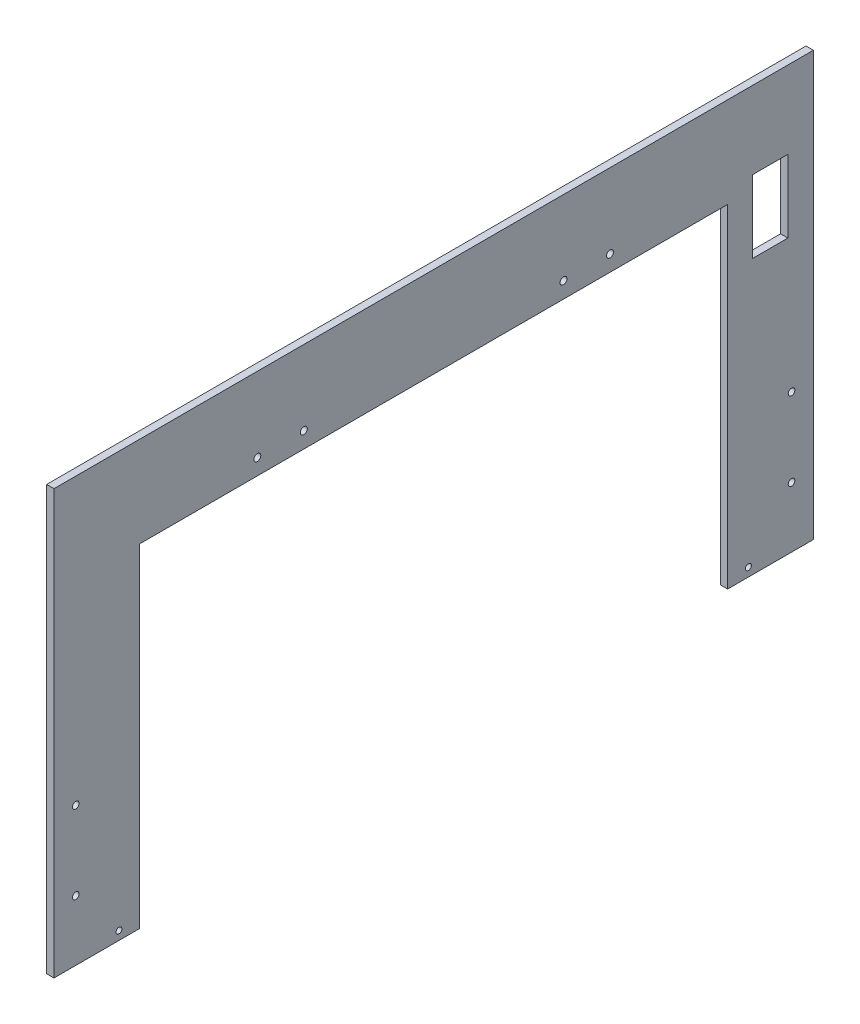
SolidWorks part; units mm, degrees
ref_plane "Front Plane" through (0, 0, 0) normal (0, 0, 1) x (1, 0, 0)
ref_plane "Top Plane" through (0, 0, 0) normal (0, 1, 0) x (1, 0, 0)
ref_plane "Right Plane" through (0, 0, 0) normal (1, 0, 0) x (0, 0, -1)
sketch "Sketch1" plane through (0, 0, 0) normal (1, 0, 0) x (0, 0, -1)
  line L1 (-246.0625, -137.3187) -> (246.0625, -137.3187)
  line L2 (-246.0625, -137.3187) -> (-246.0625, 137.3188)
  line L3 (-246.0625, 137.3188) -> (246.0625, 137.3188)
  line L4 (246.0625, -137.3187) -> (246.0625, 137.3188)
  line L5 (-246.0625, -137.3187) -> (246.0625, 137.3188) construction
  line L6 (-246.0625, 137.3188) -> (246.0625, -137.3187) construction
  point P0 (0, 0)
  dimension "D1" = 274.6375
  dimension "D2" = 492.125
extrude "Boss-Extrude1" add sketch "Sketch1" along normal blind 4.7625
sketch "Sketch2" plane through (4.7625, 0, 0) normal (1, 0, 0) x (0, 0, -1)
  line L0 (0, 0) -> (42.4264, 42.4264) construction
  line L1 (-24.8528, -60) -> (24.8528, -60)
  line L2 (-60, -24.8528) -> (-60, 24.8528)
  line L3 (-24.8528, 60) -> (24.8528, 60)
  line L4 (60, -24.8528) -> (60, 24.8528)
  line L5 (-42.4264, -42.4264) -> (42.4264, 42.4264) construction
  line L6 (0, 0) -> (-42.4264, 42.4264) construction
  line L7 (-42.4264, 42.4264) -> (-24.8528, 60) construction
  line L8 (0, 0) -> (42.4264, -42.4264) construction
  line L9 (-42.4264, 42.4264) -> (-60, 24.8528) construction
  line L10 (42.4264, -42.4264) -> (24.8528, -60) construction
  line L11 (42.4264, -42.4264) -> (60, -24.8528) construction
  line L12 (0, 0) -> (0, 60) construction
  line L13 (0, 0) -> (0, -60) construction
  line L14 (42.4264, 42.4264) -> (60, 24.8528) construction
  line L15 (42.4264, 42.4264) -> (24.8528, 60) construction
  line L16 (-42.4264, -42.4264) -> (-24.8528, -60) construction
  line L17 (-42.4264, -42.4264) -> (-60, -24.8528) construction
  line L18 (-24.8528, 60) -> (-60, 24.8528)
  line L19 (24.8528, 60) -> (60, 24.8528)
  line L20 (42.4264, -42.4264) -> (60, -24.8528)
  line L21 (24.8528, -60) -> (42.4264, -42.4264)
  line L22 (-60, -24.8528) -> (-24.8528, -60)
  point P0 (0, 0)
  dimension "D2" = 60
extrude "Cut-Extrude1" cut sketch "Sketch2" against normal up to next
sketch "Sketch3" plane through (0, 0, 246.0625) normal (0, 0, 1) x (1, 0, 0)
  line L1 (0, 137.3188) -> (4.7625, 137.3188)
  line L2 (0, 137.3188) -> (0, -137.3187)
  line L3 (0, -137.3187) -> (4.7625, -137.3187)
  line L4 (4.7625, 137.3188) -> (4.7625, -137.3187)
extrude "Boss-Extrude2" add sketch "Sketch3" against normal up to next
hole_wizard "#8 Clearance Hole1" positions "Sketch5" profile "Sketch4" hole size "#8" standard "ANSI Inch"
sketch "Sketch5" plane through (4.7625, 0, 0) normal (1, 0, 0) x (0, 0, -1)
  line L1 (-246.0625, 137.3188) -> (-246.0625, -137.3187) construction
  line L2 (-246.0625, -137.3187) -> (246.0625, -137.3187) construction
  line L3 (246.0625, -137.3187) -> (246.0625, 137.3188) construction
  point P0 (-231.9338, -98.2027)
  point P2 (-231.9338, -47.4027)
  point P4 (231.9337, -47.4027)
  point P6 (231.9337, -98.2027)
  dimension "D1" = 14.1287
  dimension "D2" = 89.916
  dimension "D3" = 39.116
  dimension "D4" = 14.1288
sketch "Sketch4" plane through (4.7625, -98.2027, 231.9338) normal (0, 1, 0) x (0, 0, -1)
  line L0 (0, 0) -> (0, 75.7154)
  line L1 (0, 75.7154) -> (2.1526, 74.422)
  line L2 (2.1526, 74.422) -> (2.1526, 0)
  line L5 (2.1526, 0) -> (0, 0)
  line L10 (0, 75.7154) -> (-2.1527, 74.422) construction
  line L11 (0, -6.35) -> (0, 107.95) construction
  dimension "Hole Dia." = 4.3053
  dimension "Hole Depth" = 74.422
  dimension "Drill Angle" = 118
sketch "Sketch9" plane through (4.7625, 0, 0) normal (1, 0, 0) x (0, 0, -1)
  line L0 (-246.0625, -137.3187) -> (246.0625, -137.3187) construction
  line L1 (-190.5, -137.3187) -> (190.5, -137.3187)
  line L2 (-190.5, -137.3187) -> (-190.5, 78.5813)
  line L3 (-190.5, 78.5813) -> (190.5, 78.5813)
  line L4 (190.5, -137.3187) -> (190.5, 78.5813)
  point P6 (0, 78.5813)
  dimension "D1" = 381
  dimension "D2" = 215.9
extrude "Cut-Extrude2" cut sketch "Sketch9" against normal through all
hole_wizard "#8 Clearance Hole2" positions "Sketch11" profile "Sketch10" hole size "#8" standard "ANSI Inch"
sketch "Sketch11" plane through (4.7625, 0, 0) normal (1, 0, 0) x (0, 0, -1)
  line L0 (-190.5, 78.5813) -> (-190.5, -137.3187) construction
  line L1 (190.5, -137.3187) -> (190.5, 78.5813) construction
  line L2 (190.5, 78.5813) -> (-190.5, 78.5813) construction
  point P0 (-114.3, 88.9)
  point P2 (-84.1375, 88.9)
  point P4 (84.1375, 88.9)
  point P6 (114.3, 88.9)
  dimension "D1" = 76.2
  dimension "D2" = 30.1625
  dimension "D3" = 30.1625
  dimension "D4" = 76.2
  dimension "D5" = 10.3187
sketch "Sketch10" plane through (4.7625, 88.9, 114.3) normal (0, 1, 0) x (0, 0, -1)
  line L0 (0, 0) -> (0, 75.7727)
  line L1 (0, 75.7727) -> (2.2479, 74.422)
  line L2 (2.2479, 74.422) -> (2.2479, 0)
  line L5 (2.2479, 0) -> (0, 0)
  line L10 (0, 75.7727) -> (-2.2479, 74.422) construction
  line L11 (0, -6.35) -> (0, 107.95) construction
  dimension "Hole Dia." = 4.4958
  dimension "Hole Depth" = 74.422
  dimension "Drill Angle" = 118
hole_wizard "#6 Clearance Hole1" positions "Sketch13" profile "Sketch12" hole size "#6" standard "ANSI Inch"
sketch "Sketch13" plane through (4.7625, 0, 0) normal (1, 0, 0) x (0, 0, -1)
  line L0 (-246.0625, -137.3187) -> (-190.5, -137.3187) construction
  line L1 (-190.5, 78.5813) -> (-190.5, -137.3187) construction
  line L2 (190.5, -137.3187) -> (190.5, 78.5813) construction
  point P0 (-203.9709, -131.7307)
  point P2 (203.9709, -131.7307)
  dimension "D1" = 5.588
  dimension "D2" = 13.4709
  dimension "D3" = 13.4709
sketch "Sketch12" plane through (4.7625, -131.7307, 203.9709) normal (0, 1, 0) x (0, 0, -1)
  line L0 (0, 0) -> (0, 75.5628)
  line L1 (0, 75.5628) -> (1.8986, 74.422)
  line L2 (1.8986, 74.422) -> (1.8986, 0)
  line L5 (1.8986, 0) -> (0, 0)
  line L10 (0, 75.5628) -> (-1.8987, 74.422) construction
  line L11 (0, -6.35) -> (0, 107.95) construction
  dimension "Hole Dia." = 3.7973
  dimension "Hole Depth" = 74.422
  dimension "Drill Angle" = 118
sketch "Sketch14" plane through (4.7625, 0, 0) normal (1, 0, 0) x (0, 0, -1)
  line L0 (246.0625, -137.3187) -> (246.0625, 137.3188) construction
  line L1 (206.6925, 87.1538) -> (229.5525, 87.1538)
  line L2 (206.6925, 87.1538) -> (206.6925, 40.1638)
  line L3 (206.6925, 40.1638) -> (229.5525, 40.1638)
  line L4 (229.5525, 87.1538) -> (229.5525, 40.1638)
  line L5 (206.6925, 87.1538) -> (229.5525, 40.1638) construction
  line L6 (206.6925, 40.1638) -> (229.5525, 87.1538) construction
  line L7 (246.0625, 137.3188) -> (-246.0625, 137.3188) construction
  point P0 (218.1225, 63.6588)
  dimension "D1" = 22.86
  dimension "D2" = 46.99
  dimension "D3" = 27.94
  dimension "D4" = 73.66
extrude "Cut-Extrude3" cut sketch "Sketch14" against normal blind 46.736
